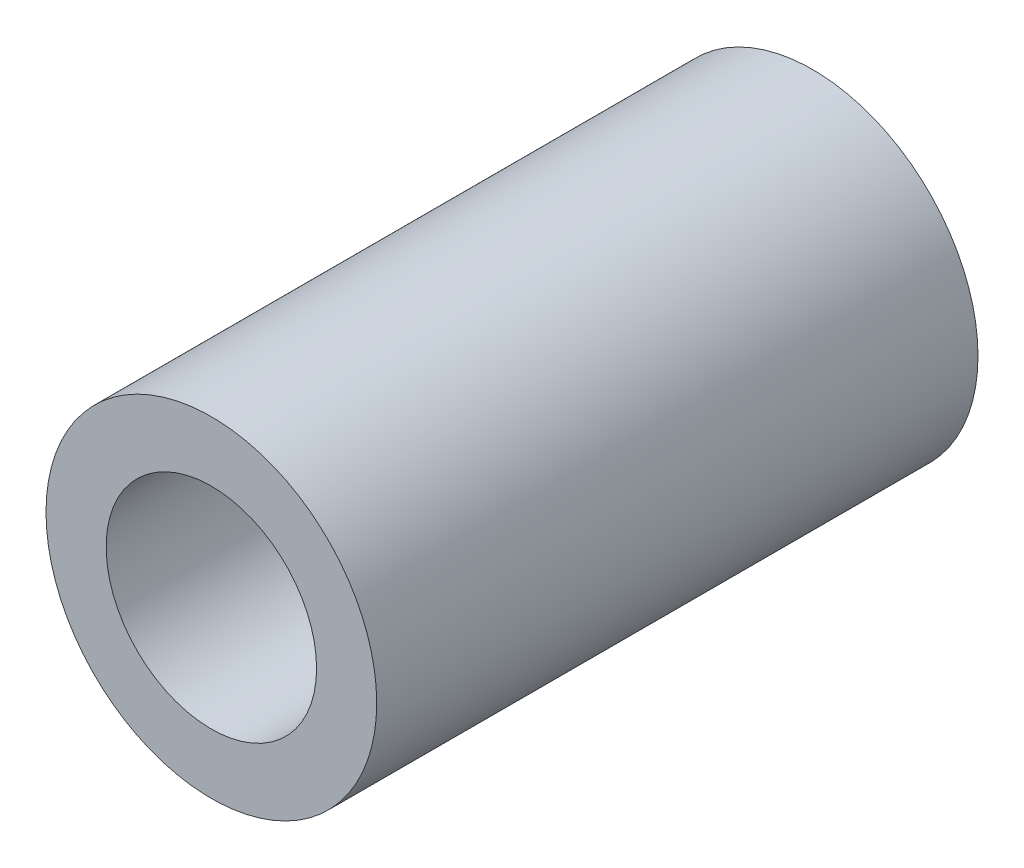
SolidWorks part; units mm, degrees
ref_plane "Front Plane" through (0, 0, 0) normal (0, 0, 1) x (1, 0, 0)
ref_plane "Top Plane" through (0, 0, 0) normal (0, 1, 0) x (1, 0, 0)
ref_plane "Right Plane" through (0, 0, 0) normal (1, 0, 0) x (0, 0, -1)
sketch "Sketch1" plane through (0, 0, 0) normal (0, 0, 1) x (1, 0, 0)
  circle A1 centre (-103.0201, 119.3649) radius 1.75
  circle A2 centre (-103.0201, 119.3649) radius 2.75
  dimension "D1" = 1
extrude "Boss-Extrude1" add sketch "Sketch1" along normal blind 10
